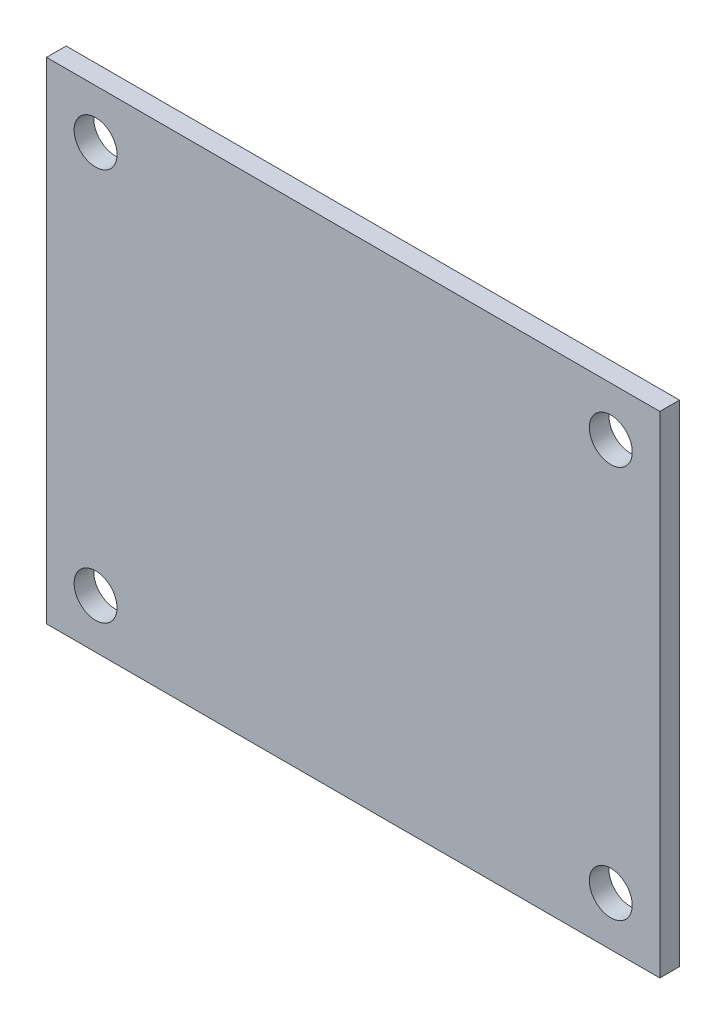
SolidWorks part; units mm, degrees
ref_plane "Plan de face" through (0, 0, 0) normal (0, 0, 1) x (1, 0, 0)
ref_plane "Plan de dessus" through (0, 0, 0) normal (0, 1, 0) x (1, 0, 0)
ref_plane "Plan de droite" through (0, 0, 0) normal (1, 0, 0) x (0, 0, -1)
sketch "Model" plane through (0, 0, 0) normal (0, 0, 1) x (1, 0, 0)
  line L0 (0, 0) -> (50, 0)
  line L1 (50, 0) -> (50, 40)
  line L2 (50, 40) -> (0, 40)
  line L3 (0, 40) -> (0, 0)
  circle A0 centre (4, 4) radius 1.75
  circle A1 centre (46, 4) radius 1.75
  circle A2 centre (46, 36) radius 1.75
  circle A3 centre (4, 36) radius 1.75
  dimension "D4" = 4
  dimension "D1" = 50
  dimension "D2" = 40
  dimension "D3" = 4
extrude "Boss.-Extru.1" add sketch "Model" along normal blind 1.6
